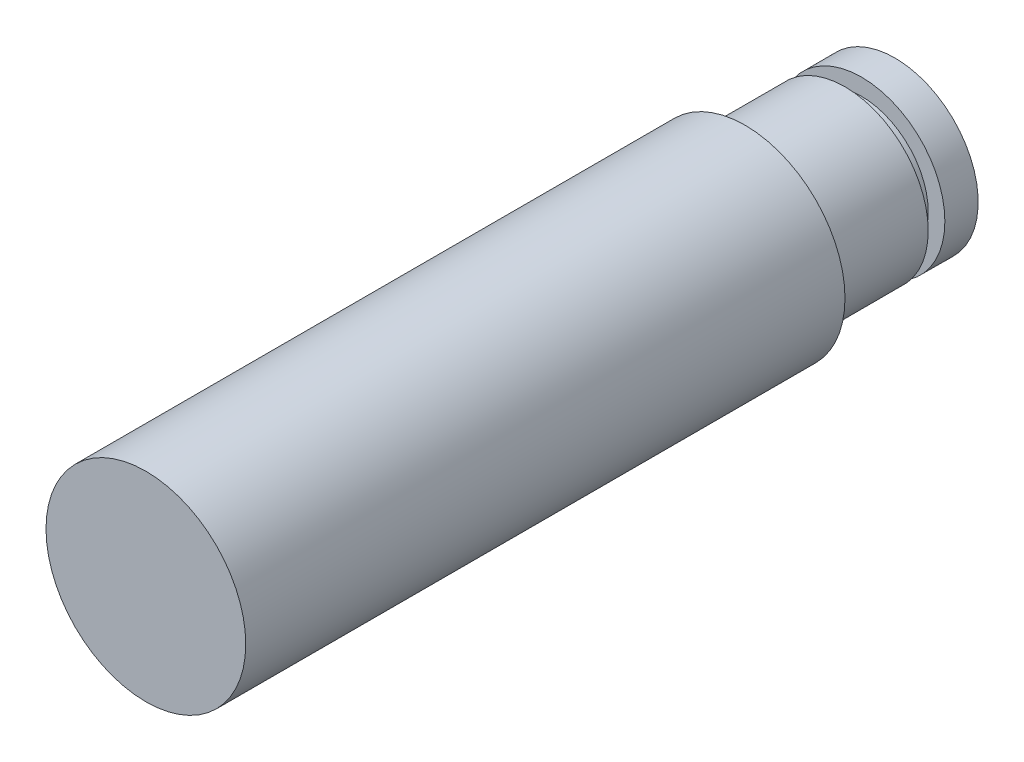
SolidWorks part; units mm, degrees
material "1.0036 (S235JRG1)"
ref_plane "Front Plane" through (0, 0, 0) normal (0, 0, 1) x (1, 0, 0)
ref_plane "Top Plane" through (0, 0, 0) normal (0, 1, 0) x (1, 0, 0)
ref_plane "Right Plane" through (0, 0, 0) normal (1, 0, 0) x (0, 0, -1)
sketch "Sketch1" plane through (0, 0, 0) normal (0, 0, 1) x (1, 0, 0)
  circle A0 centre (0, 0) radius 12
  dimension "D1" = 24
extrude "Boss-Extrude1" add sketch "Sketch1" along normal blind 90
sketch "Sketch2" plane through (0, 0, 0) normal (0, 0, -1) x (-1, 0, 0)
  circle A0 centre (0, 0) radius 10
  circle A1 centre (0, 0) radius 12
extrude "Cut-Extrude2" cut sketch "Sketch2" against normal blind 18
sketch "Sketch3" plane through (0, 0, 0) normal (1, 0, 0) x (0, 0, -1)
  line L0 (-18, 10) -> (-18, -10)
  line L1 (-18, -12) -> (-18, 12) construction
  line L2 (-18, -10) -> (-18, 10) construction
  line L3 (-18, 10) -> (-6, 10)
  line L4 (0, 10) -> (-18, 10) construction
  line L5 (-18, 0) -> (0, 0) construction
  line L6 (-6, 10) -> (-4, 10)
  line L7 (-6, 10) -> (-6, 8)
  line L8 (-6, 8) -> (-4, 8)
  line L9 (-4, 10) -> (-4, 8)
revolve "Cut-Revolve1" cut sketch "Sketch3" angle 360 about L5
